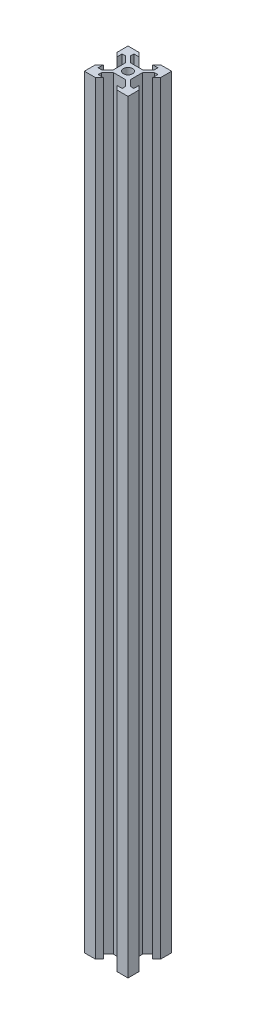
SolidWorks part; units mm, degrees
material "6061-T6 (SS)"
ref_plane "前视基准面" through (0, 0, 0) normal (0, 0, 1) x (1, 0, 0)
ref_plane "上视基准面" through (0, 0, 0) normal (0, 1, 0) x (1, 0, 0)
ref_plane "右视基准面" through (0, 0, 0) normal (1, 0, 0) x (0, 0, -1)
sketch "草图1" plane through (0, 0, 0) normal (0, 1, 0) x (1, 0, 0)
  line L0 (-10, 10) -> (-4.9, 10)
  line L1 (-10, -10) -> (10, -10) construction
  line L2 (-10, -10) -> (-10, 10) construction
  line L3 (-10, 10) -> (10, 10) construction
  line L4 (10, -10) -> (10, 10) construction
  line L5 (-10, -10) -> (10, 10) construction
  line L6 (-10, 10) -> (10, -10) construction
  line L7 (-4.9, 10) -> (-3.1, 8.2)
  line L8 (-3.1, 8.2) -> (-5.5, 8.2)
  line L9 (-5.5, 8.2) -> (-5.5, 6.5607)
  line L10 (-5.5, 6.5607) -> (-2.8393, 3.9)
  line L11 (-2.8393, 3.9) -> (0, 3.9)
  line L12 (0, 0) -> (0, 10) construction
  line L13 (-3.9, 2.8393) -> (-3.9, -2.8393)
  line L14 (-6.5607, 5.5) -> (-3.9, 2.8393)
  line L15 (-8.2, 5.5) -> (-6.5607, 5.5)
  line L16 (-8.2, 3.1) -> (-8.2, 5.5)
  line L17 (-10, 4.9) -> (-8.2, 3.1)
  line L18 (-10, 10) -> (-10, 4.9)
  line L19 (2.8393, 3.9) -> (0, 3.9)
  line L20 (10, 10) -> (10, 4.9)
  line L21 (10, 4.9) -> (8.2, 3.1)
  line L22 (8.2, 3.1) -> (8.2, 5.5)
  line L23 (8.2, 5.5) -> (6.5607, 5.5)
  line L24 (6.5607, 5.5) -> (3.9, 2.8393)
  line L25 (3.9, 2.8393) -> (3.9, -2.8393)
  line L26 (5.5, 6.5607) -> (2.8393, 3.9)
  line L27 (5.5, 8.2) -> (5.5, 6.5607)
  line L28 (3.1, 8.2) -> (5.5, 8.2)
  line L29 (4.9, 10) -> (3.1, 8.2)
  line L30 (10, 10) -> (4.9, 10)
  line L31 (-10, 0) -> (10, 0) construction
  line L32 (10, -10) -> (10, -4.9)
  line L33 (10, -10) -> (4.9, -10)
  line L34 (4.9, -10) -> (3.1, -8.2)
  line L35 (-4.9, -10) -> (-3.1, -8.2)
  line L36 (-10, -10) -> (-4.9, -10)
  line L37 (-10, -10) -> (-10, -4.9)
  line L38 (3.1, -8.2) -> (5.5, -8.2)
  line L39 (5.5, -8.2) -> (5.5, -6.5607)
  line L40 (5.5, -6.5607) -> (2.8393, -3.9)
  line L41 (6.5607, -5.5) -> (3.9, -2.8393)
  line L42 (8.2, -5.5) -> (6.5607, -5.5)
  line L43 (8.2, -3.1) -> (8.2, -5.5)
  line L44 (10, -4.9) -> (8.2, -3.1)
  line L45 (2.8393, -3.9) -> (0, -3.9)
  line L46 (-10, -4.9) -> (-8.2, -3.1)
  line L47 (-8.2, -3.1) -> (-8.2, -5.5)
  line L48 (-8.2, -5.5) -> (-6.5607, -5.5)
  line L49 (-6.5607, -5.5) -> (-3.9, -2.8393)
  line L50 (-2.8393, -3.9) -> (0, -3.9)
  line L51 (-5.5, -6.5607) -> (-2.8393, -3.9)
  line L52 (-5.5, -8.2) -> (-5.5, -6.5607)
  line L53 (-3.1, -8.2) -> (-5.5, -8.2)
  circle A0 centre (0, 0) radius 2.1
  point P0 (0, 0)
  point P23 (-1.4197, 3.9)
  point P24 (1.4197, 3.9)
  point P42 (-3.9, 0)
  point P43 (3.9, 0)
  point P56 (1.4197, -3.9)
  dimension "D9" = 4.2
  dimension "D1" = 20
  dimension "D2" = 20
  dimension "D3" = 0.75
  dimension "D4" = 1.8
  dimension "D5" = 4.9
  dimension "D6" = 3.1
  dimension "D7" = 5.5
  dimension "D8" = 6.1
extrude "凸台-拉伸1" add sketch "草图1" along normal blind 350
